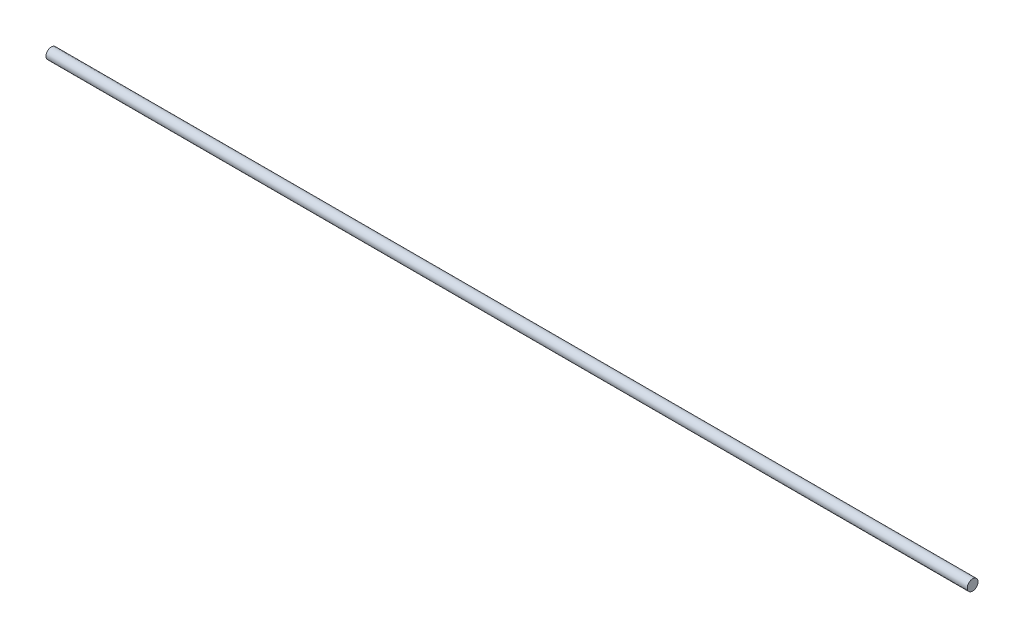
SolidWorks part; units mm, degrees
ref_plane "Front Plane" through (0, 0, 0) normal (0, 0, 1) x (1, 0, 0)
ref_plane "Top Plane" through (0, 0, 0) normal (0, 1, 0) x (1, 0, 0)
ref_plane "Right Plane" through (0, 0, 0) normal (1, 0, 0) x (0, 0, -1)
sketch "Sketch1" plane through (0, 0, 0) normal (1, 0, 0) x (0, 0, -1)
  circle A0 centre (0, 0) radius 1.778
  dimension "D1" = 3.556
extrude "Boss-Extrude1" add sketch "Sketch1" along normal mid plane 304.8
equation "\"HingeLength\"=12"
equation "\"D1@Boss-Extrude1\"=\"HingeLength\""
